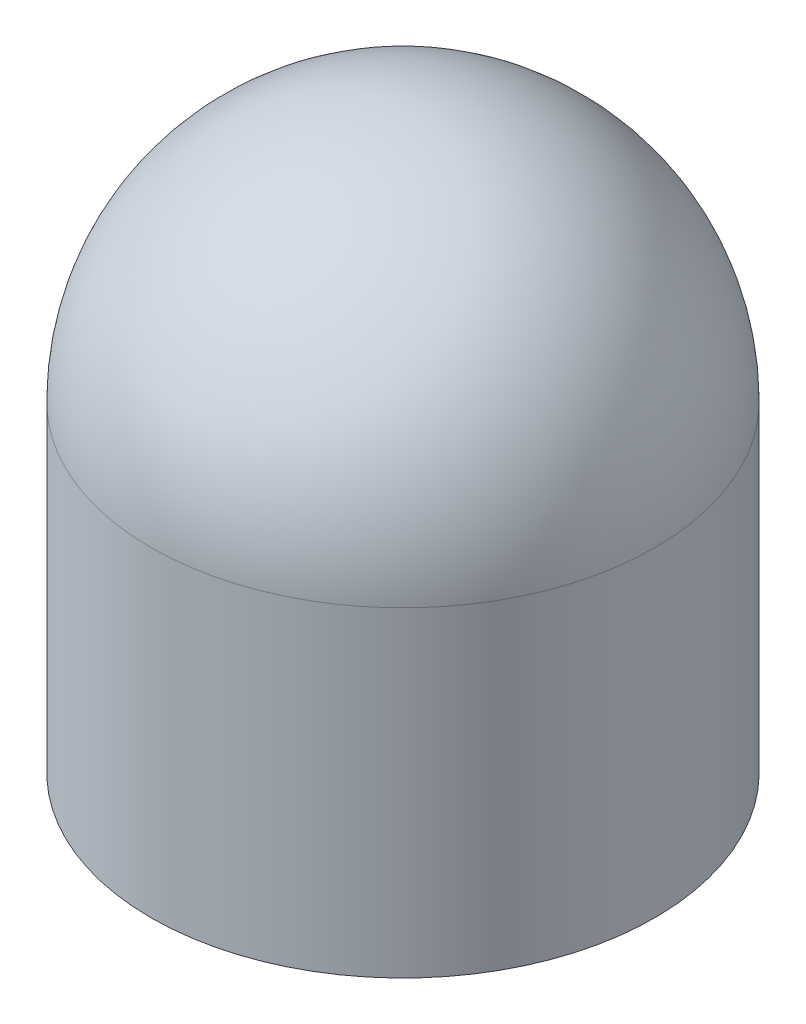
SolidWorks part; units mm, degrees
material "6061-T6 (SS)"
ref_plane "Front Plane" through (0, 0, 0) normal (0, 0, 1) x (1, 0, 0)
ref_plane "Top Plane" through (0, 0, 0) normal (0, 1, 0) x (1, 0, 0)
ref_plane "Right Plane" through (0, 0, 0) normal (1, 0, 0) x (0, 0, -1)
sketch "Sketch1" plane through (0, 0, 0) normal (0, 0, 1) x (1, 0, 0)
  line L0 (69.85, 0) -> (69.85, 76.2)
  line L1 (63.5, 76.2) -> (63.5, 0)
  line L2 (63.5, 0) -> (69.85, 0)
  line L3 (0, 146.05) -> (0, 139.7)
  line L5 (69.85, 0) -> (66.675, 0)
  line L6 (69.85, 0) -> (69.85, -12.7)
  line L7 (69.85, -12.7) -> (66.675, -12.7)
  line L8 (66.675, 0) -> (66.675, -12.7)
  arc A0 (63.5, 76.2) -> (0, 139.7) centre (0, 76.2) ccw
  arc A1 (69.85, 76.2) -> (0, 146.05) centre (0, 76.2) ccw
  dimension "D3" = 127
  dimension "D1" = 76.2
  dimension "D2" = 63.5
  dimension "D4" = 3.175
  dimension "D5" = 6.35
  dimension "D6" = 12.7
revolve "Revolve3" add sketch "Sketch1" angle 360 about L3
sketch "Sketch2" plane through (0, 0, 0) normal (0, -1, 0) x (-1, 0, 0)
  circle A0 centre (0, 0) radius 65.0875
  circle A1 centre (0, 0) radius 66.675 construction
  circle A2 centre (0, 0) radius 66.675
  dimension "D1" = 1.5875
extrude "Boss-Extrude1" add sketch "Sketch2" along normal blind 11.1125
sketch3d "3DSketch1"
  circle A1 centre (0, -11.1125, 0) radius 66.675
  circle A2 centre (0, -11.1125, 0) radius 66.675
  point P5 (0, -77.7875, 0)
  point P7 (0, -77.7875, 0)
  dimension "D1" = 0
